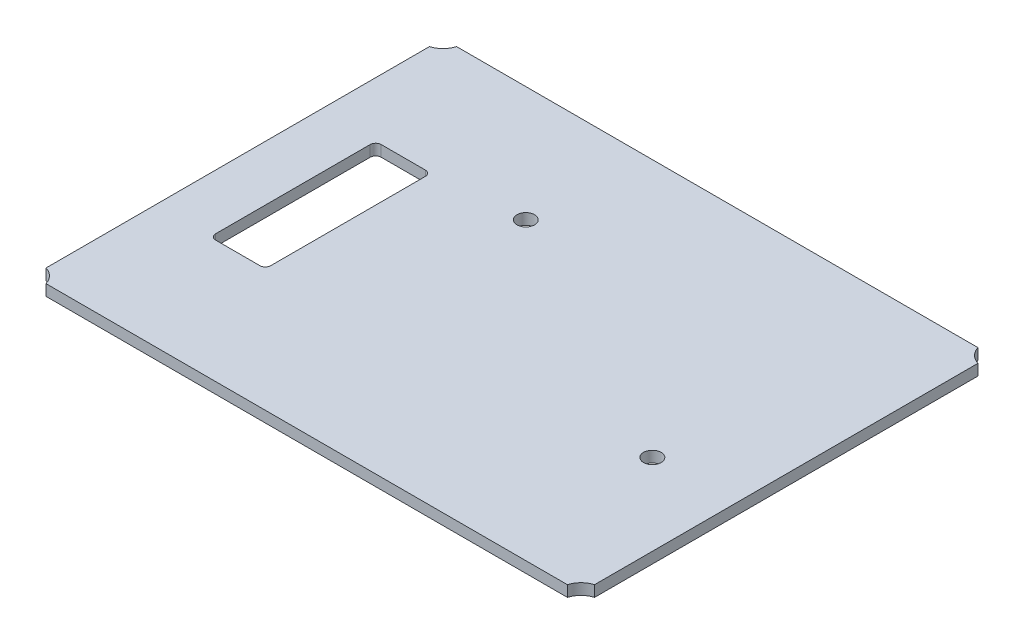
SolidWorks part; units mm, degrees
ref_plane "Front Plane" through (0, 0, 0) normal (0, 0, 1) x (1, 0, 0)
ref_plane "Top Plane" through (0, 0, 0) normal (0, 1, 0) x (1, 0, 0)
ref_plane "Right Plane" through (0, 0, 0) normal (1, 0, 0) x (0, 0, -1)
sketch "Sketch1" plane through (0, 0, 0) normal (0, 1, 0) x (1, 0, 0)
  line L0 (0, 37.2) -> (0, -37.2) construction
  line L1 (-49.7, -37.2) -> (49.7, -37.2)
  line L2 (-49.7, -37.2) -> (-49.7, 37.2)
  line L3 (-49.7, 37.2) -> (49.7, 37.2)
  line L4 (49.7, -37.2) -> (49.7, 37.2)
  line L5 (-49.7, -37.2) -> (49.7, 37.2) construction
  line L6 (-49.7, 37.2) -> (49.7, -37.2) construction
  line L7 (-49.7, 0) -> (49.7, 0) construction
  line L8 (0, 0) -> (-49.7, 37.2) construction
  circle A2 centre (-50.7, 38.2) radius 3.6
  circle A3 centre (50.7, 38.2) radius 3.6
  circle A4 centre (50.7, -38.2) radius 3.6
  circle A5 centre (-50.7, -38.2) radius 3.6
  point P0 (0, 0)
  dimension "D3" = 7.2
  dimension "D1" = 74.4
  dimension "D2" = 99.4
  dimension "D4" = 1
  dimension "D5" = 1
extrude "Boss-Extrude1" add sketch "Sketch1" along normal blind 2 contours L2 A5 L1 A4 L4 A3 L3 A2
sketch "Sketch2" plane through (0, 2, 0) normal (0, 1, 0) x (1, 0, 0)
  line L0 (-49.7, 0) -> (49.7, 0) construction
  line L1 (-49.7, -34.7417) -> (-49.7, 34.7417) construction
  line L2 (49.7, -34.7417) -> (49.7, 34.7417) construction
  line L4 (-39.7, -15) -> (-29.7, -15)
  line L5 (-39.7, -15) -> (-39.7, 15)
  line L6 (-39.7, 15) -> (-29.7, 15)
  line L7 (-29.7, -15) -> (-29.7, 15)
  line L8 (-39.7, -15) -> (-29.7, 15) construction
  line L9 (-39.7, 15) -> (-29.7, -15) construction
  point P6 (-34.7, 0)
  dimension "D1" = 10
  dimension "D2" = 30
  dimension "D3" = 15
extrude "Cut-Extrude1" cut sketch "Sketch2" against normal through all
fillet "Fillet1" radius 1 4 edges at (-29.7, 1, 15) (-39.7, 1, 15) (-29.7, 1, -15) (-39.7, 1, -15)
sketch "Sketch3" plane through (0, 2, 0) normal (0, 1, 0) x (1, 0, 0)
  circle A0 centre (-13.7947, 16.2907) radius 1.6
  circle A1 centre (34.9733, -9.5413) radius 1.6
extrude "Cut-Extrude2" cut sketch "Sketch3" against normal up to next
